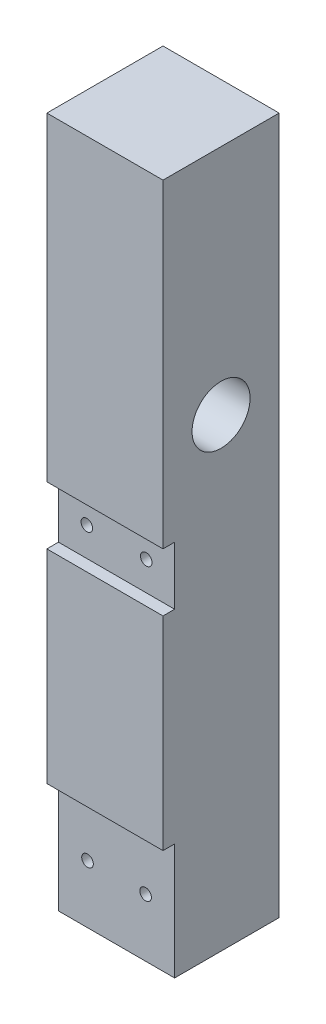
SolidWorks part; units mm, degrees
ref_plane "Front Plane" through (0, 0, 0) normal (0, 0, 1) x (1, 0, 0)
ref_plane "Top Plane" through (0, 0, 0) normal (0, 1, 0) x (1, 0, 0)
ref_plane "Right Plane" through (0, 0, 0) normal (1, 0, 0) x (0, 0, -1)
sketch "Sketch1" plane through (0, 0, 0) normal (1, 0, 0) x (0, 0, -1)
  line L0 (0, 55) -> (0, -55) construction
  line L1 (0, 120) -> (20, 120)
  line L2 (0, 120) -> (0, 0)
  line L3 (0, 0) -> (20, 0)
  line L4 (20, 120) -> (20, 0)
  line L5 (55, 0) -> (-55, 0) construction
  circle A2 centre (10, 80) radius 2.5
  dimension "D3" = 5
  dimension "D4" = 40
  dimension "D5" = 10
  dimension "D1" = 20
  dimension "D2" = 120
extrude "Boss-Extrude2" add sketch "Sketch1" against normal blind 20
ref_plane "Plane1" through (0, 0, 0) normal (1, 0, 0) x (0, 0, -1)
sketch "Sketch10" plane through (0, 0, 0) normal (1, 0, 0) x (0, 0, -1)
  circle A0 centre (10, 80) radius 5
  dimension "D1" = 10
extrude "Cut-Extrude1" cut sketch "Sketch10" against normal blind 10
ref_plane "Plane2" through (0, 0, 0) normal (0, 0, 1) x (1, 0, 0)
sketch "Sketch11" plane through (0, 0, 0) normal (0, 0, 1) x (1, 0, 0)
  line L0 (-10, 120) -> (-10, 0)
  line L1 (-20, 120) -> (0, 120) construction
  line L2 (11, 0) -> (-11, 0) construction
  line L3 (-20, 120) -> (-20, 0) construction
  line L4 (-20, 0) -> (0, 0) construction
  circle A0 centre (-15, 10) radius 1
  circle A1 centre (-5, 10) radius 1
  dimension "D1" = 2
  dimension "D2" = 5
  dimension "D3" = 10
extrude "Cut-Extrude2" cut sketch "Sketch11" against normal through all contours A0 | A1
ref_plane "Plane3" through (0, 0, -20) normal (0, 0, -1) x (-1, 0, 0)
sketch "Sketch12" plane through (0, 0, -20) normal (0, 0, -1) x (-1, 0, 0)
  circle A0 centre (5, 10) radius 2
  circle A1 centre (15, 10) radius 2
  dimension "D1" = 4
  dimension "D2" = 4
extrude "Cut-Extrude3" cut sketch "Sketch12" against normal blind 5
ref_plane "Plane4" through (0, 0, -20) normal (0, 0, -1) x (-1, 0, 0)
sketch "Sketch13" plane through (0, 0, -20) normal (0, 0, -1) x (-1, 0, 0)
  line L0 (10, 120) -> (10, 0)
  line L1 (20, 120) -> (0, 120) construction
  line L2 (11, 0) -> (-11, 0) construction
  circle A0 centre (4.8805, 60) radius 1
  circle A1 centre (15.1195, 60) radius 1
  dimension "D1" = 2
  dimension "D2" = 60
extrude "Cut-Extrude4" cut sketch "Sketch13" against normal through all contours A0 | A1
ref_plane "Plane5" through (0, 0, -20) normal (0, 0, -1) x (-1, 0, 0)
sketch "Sketch14" plane through (0, 0, -20) normal (0, 0, -1) x (-1, 0, 0)
  circle A0 centre (4.8805, 60) radius 2
  circle A1 centre (15.1195, 60) radius 2
  dimension "D1" = 4
  dimension "D2" = 4
extrude "Cut-Extrude5" cut sketch "Sketch14" against normal blind 5
ref_plane "Plane6" through (0, 0, 0) normal (0, 0, 1) x (1, 0, 0)
sketch "Sketch16" plane through (0, 0, 0) normal (0, 0, 1) x (1, 0, 0)
  line L0 (11, 0) -> (-11, 0) construction
  line L1 (-20, 65) -> (0, 65)
  line L2 (-20, 65) -> (-20, 55)
  line L3 (-20, 55) -> (0, 55)
  line L4 (0, 65) -> (0, 55)
  line L5 (-20, 65) -> (0, 55) construction
  line L6 (-20, 55) -> (0, 65) construction
  line L7 (-20, 120) -> (-20, 0) construction
  line L8 (0, -11) -> (0, 11) construction
  line L9 (-20, 20) -> (0, 20)
  line L10 (-20, 20) -> (-20, 0)
  line L11 (-20, 0) -> (0, 0)
  line L12 (0, 20) -> (0, 0)
  line L13 (-20, 20) -> (0, 0) construction
  line L14 (-20, 0) -> (0, 20) construction
  point P0 (-10, 60)
  point P9 (-10, 10)
  dimension "D1" = 60
  dimension "D2" = 10
  dimension "D3" = 10
  dimension "D4" = 20
  dimension "D5" = 10
extrude "Cut-Extrude6" cut sketch "Sketch16" against normal blind 2
